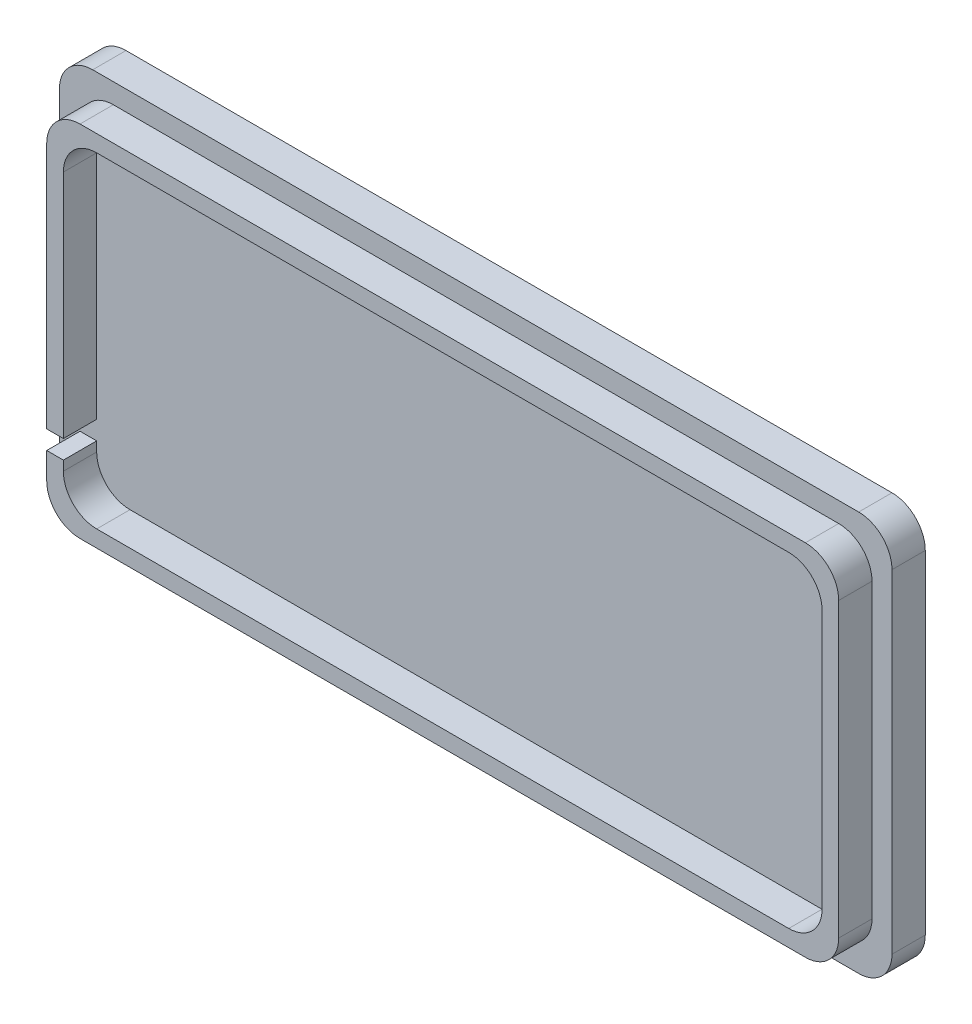
SolidWorks part; units mm, degrees
material "ABS"
ref_plane "Front Plane" through (0, 0, 0) normal (0, 0, 1) x (1, 0, 0)
ref_plane "Top Plane" through (0, 0, 0) normal (0, 1, 0) x (1, 0, 0)
ref_plane "Right Plane" through (0, 0, 0) normal (1, 0, 0) x (0, 0, -1)
sketch "Sketch2" plane through (0, 0, 0) normal (0, 0, 1) x (1, 0, 0)
  line L1 (-151.003, 68.453) -> (151.003, 68.453)
  line L2 (-151.003, 68.453) -> (-151.003, -68.453)
  line L3 (-151.003, -68.453) -> (151.003, -68.453)
  line L4 (151.003, 68.453) -> (151.003, -68.453)
  point P4 (0, 68.453)
  point P6 (-151.003, 0)
  dimension "D1" = 302.006
  dimension "D2" = 136.906
extrude "Boss-Extrude1" add sketch "Sketch2" along normal blind 12.7
sketch "Sketch3" plane through (0, 0, 0) normal (0, 0, -1) x (-1, 0, 0)
  line L1 (158.877, -76.327) -> (-158.623, -76.327)
  line L2 (158.877, -76.327) -> (158.877, 76.073)
  line L3 (158.877, 76.073) -> (-158.623, 76.073)
  line L4 (-158.623, -76.327) -> (-158.623, 76.073)
extrude "Boss-Extrude2" add sketch "Sketch3" along normal blind 12.7
sketch "Sketch4" plane through (0, 0, 12.7) normal (0, 0, 1) x (1, 0, 0)
  line L8 (-144.653, 62.103) -> (-144.653, -62.103)
  line L9 (-144.653, -62.103) -> (144.653, -62.103)
  line L10 (144.653, -62.103) -> (144.653, 62.103)
  line L11 (144.653, 62.103) -> (-144.653, 62.103)
  line L12 (-144.653, 62.103) -> (-144.653, -62.103)
  line L13 (-144.653, -62.103) -> (144.653, -62.103)
  line L14 (144.653, -62.103) -> (144.653, 62.103)
  line L15 (144.653, 62.103) -> (-144.653, 62.103)
  dimension "D1" = 6.35
extrude "Cut-Extrude1" cut sketch "Sketch4" against normal blind 12.7
sketch "Sketch5" plane through (-151.003, 0, 0) normal (-1, 0, 0) x (0, 0, 1)
  line L11 (12.7, -45.72) -> (0, -45.72)
  line L12 (0, -76.327) -> (0, 76.073) construction
  line L13 (12.7, -38.608) -> (0, -38.608)
  line L14 (0, -45.72) -> (0, -38.608)
  arc A3 (12.7, -45.72) -> (12.7, -38.608) centre (12.7, -42.164) ccw
  dimension "D1" = 7.112
  dimension "D2" = 12.7
extrude "Cut-Extrude3" cut sketch "Sketch5" against normal up to next
fillet "Fillet1" radius 12.7 12 edges at (144.653, 62.103, 6.35) (144.653, -62.103, 6.35) (-144.653, -62.103, 6.35) (-144.653, 62.103, 6.35) (-151.003, 68.453, 6.35) (151.003, 68.453, 6.35) (151.003, -68.453, 6.35) (-151.003, -68.453, 6.35) (-158.877, -76.327, -6.35) (158.623, -76.327, -6.35) (158.623, 76.073, -6.35) (-158.877, 76.073, -6.35)
